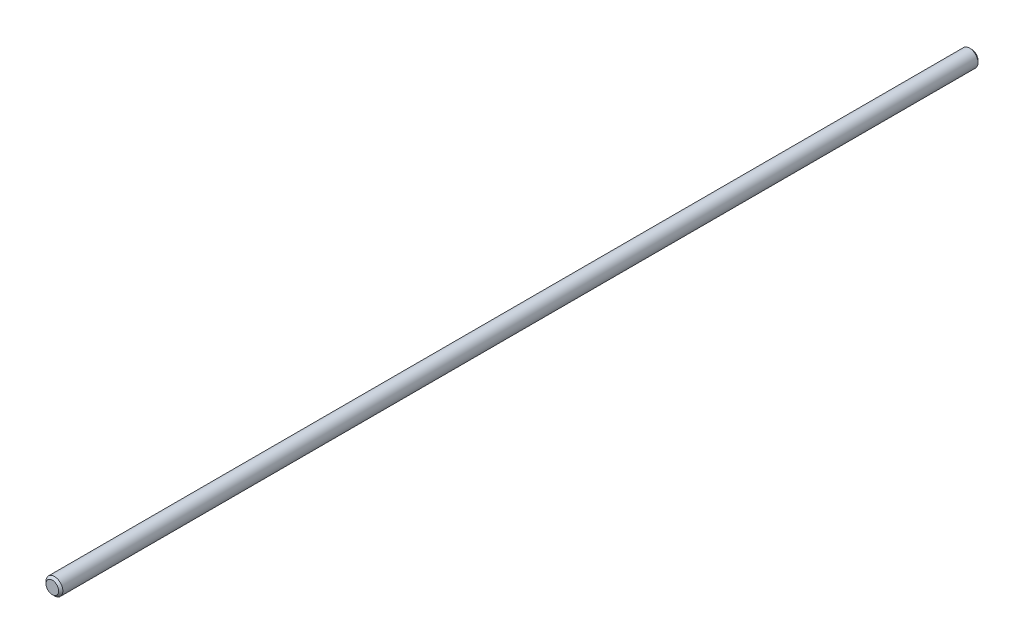
SolidWorks part; units mm, degrees
ref_plane "Front Plane" through (0, 0, 0) normal (0, 0, 1) x (1, 0, 0)
ref_plane "Top Plane" through (0, 0, 0) normal (0, 1, 0) x (1, 0, 0)
ref_plane "Right Plane" through (0, 0, 0) normal (1, 0, 0) x (0, 0, -1)
sketch "Sketch1" plane through (0, 0, 0) normal (0, 0, 1) x (1, 0, 0)
  circle A0 centre (0, 0) radius 4
  dimension "D1" = 8
extrude "Boss-Extrude1" add sketch "Sketch1" along normal blind 437
chamfer "Chamfer1" distance 1 angle 45 2 edges at (4, 0, 437) (4, 0, 0)
